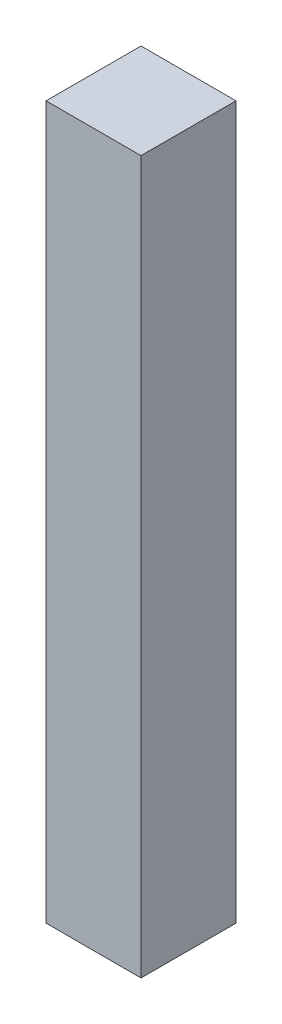
SolidWorks part; units mm, degrees
material "ABS"
ref_plane "Front Plane" through (0, 0, 0) normal (0, 0, 1) x (1, 0, 0)
ref_plane "Top Plane" through (0, 0, 0) normal (0, 1, 0) x (1, 0, 0)
ref_plane "Right Plane" through (0, 0, 0) normal (1, 0, 0) x (0, 0, -1)
sketch "Sketch1" plane through (0, 0, 0) normal (0, 1, 0) x (1, 0, 0)
  line L1 (-2.54, -2.54) -> (2.54, -2.54)
  line L2 (-2.54, -2.54) -> (-2.54, 2.54)
  line L3 (-2.54, 2.54) -> (2.54, 2.54)
  line L4 (2.54, -2.54) -> (2.54, 2.54)
  line L5 (-2.54, -2.54) -> (2.54, 2.54) construction
  line L6 (-2.54, 2.54) -> (2.54, -2.54) construction
extrude "Boss-Extrude2" add sketch "Sketch1" along normal blind 38.1 contours L3 L4 L1 L2
